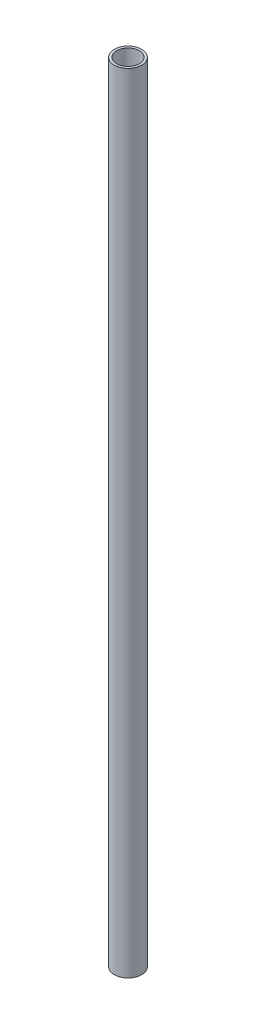
SolidWorks part; units mm, degrees
ref_plane "Front Plane" through (0, 0, 0) normal (0, 0, 1) x (1, 0, 0)
ref_plane "Top Plane" through (0, 0, 0) normal (0, 1, 0) x (1, 0, 0)
ref_plane "Right Plane" through (0, 0, 0) normal (1, 0, 0) x (0, 0, -1)
sketch "Sketch1" plane through (0, 0, 0) normal (0, 1, 0) x (1, 0, 0)
  circle A0 centre (0, 0) radius 9.525
  circle A1 centre (0, 0) radius 7.874
  dimension "D1" = 19.05
  dimension "D2" = 15.748
extrude "Boss-Extrude1" add sketch "Sketch1" along normal blind 546.1
sketch "Sketch2" plane through (603.3699, -776.6034, -147.7282) normal (-0.2389, 0, 0.9711) x (0.9711, 0, 0.2389)
  circle A1 centre (-550.6167, 782.9534) radius 1.5875
  dimension "D1" = 3.175
  dimension "D2" = 6.35
extrude "Cut-Extrude1" cut sketch "Sketch2" along normal blind 279.527
